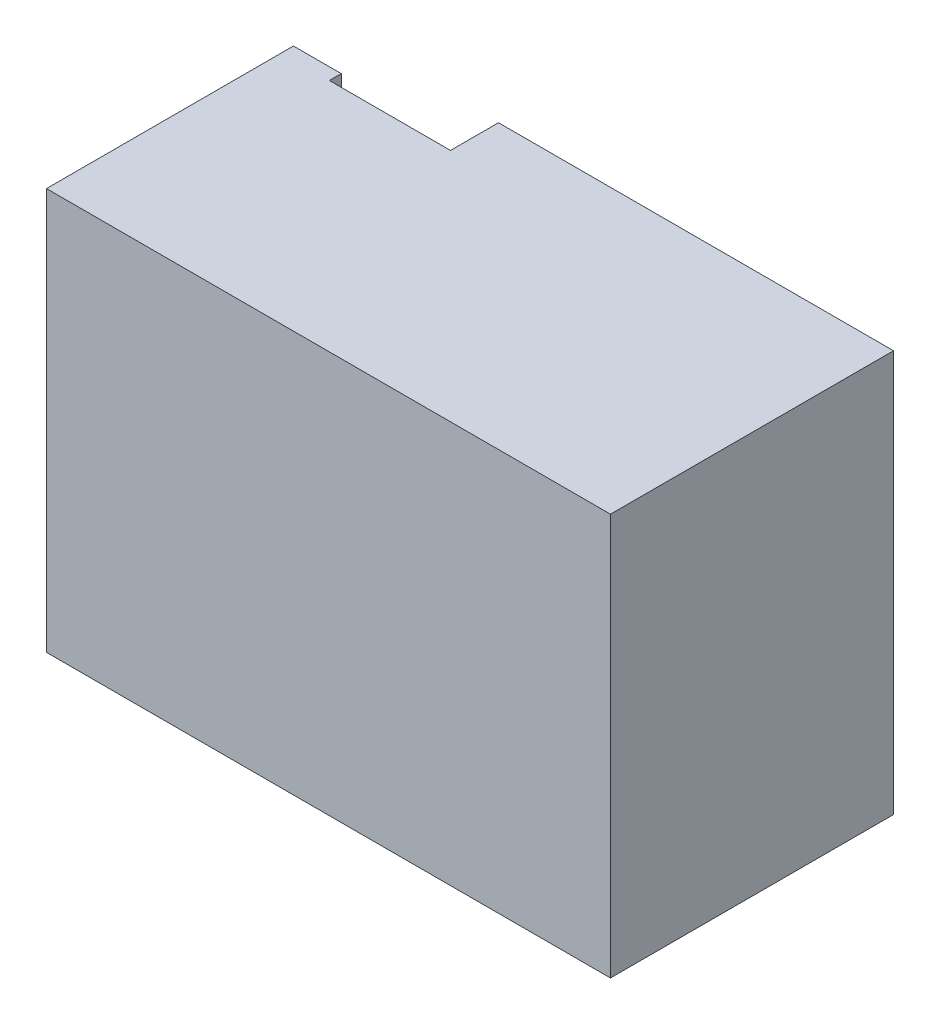
SolidWorks part; units mm, degrees
ref_plane "Front Plane" through (0, 0, 0) normal (0, 0, 1) x (1, 0, 0)
ref_plane "Top Plane" through (0, 0, 0) normal (0, 1, 0) x (1, 0, 0)
ref_plane "Right Plane" through (0, 0, 0) normal (1, 0, 0) x (0, 0, -1)
sketch "Sketch2" plane through (0, 0, 5.4923) normal (0, 0, 1) x (1, 0, 0)
  line L1 (72.3063, -48.321) -> (-33.8937, -48.321)
  line L2 (72.3063, -48.321) -> (72.3063, 59.679)
  line L3 (72.3063, 59.679) -> (-33.8937, 59.679)
  line L4 (-33.8937, -48.321) -> (-33.8937, 59.679)
extrude "Boss-Extrude1" add sketch "Sketch2" along normal blind 38.1
sketch "Sketch3" plane through (-33.8937, 0, 0) normal (-1, 0, 0) x (0, 0, 1)
  line L0 (43.5923, 59.679) -> (5.4923, 59.679) construction
  line L1 (43.5923, -48.321) -> (18.4023, -48.321)
  line L2 (43.5923, -48.321) -> (43.5923, 59.679)
  line L3 (43.5923, 59.679) -> (18.4023, 59.679)
  line L4 (18.4023, -48.321) -> (18.4023, 59.679)
  line L5 (18.4023, 59.679) -> (18.4023, -48.321) construction
extrude "Boss-Extrude2" add sketch "Sketch3" along normal up to vertex (45.43 mm away)
sketch "Sketch5" plane through (0, 0, 18.4023) normal (0, 0, -1) x (-1, 0, 0)
  line L0 (79.3237, 59.679) -> (33.8937, 59.679) construction
  line L1 (79.3237, -48.321) -> (66.4637, -48.321)
  line L2 (79.3237, -48.321) -> (79.3237, 59.679)
  line L3 (79.3237, 59.679) -> (66.4637, 59.679)
  line L4 (66.4637, -48.321) -> (66.4637, 59.679)
  line L5 (66.4637, -48.321) -> (66.4637, 59.679) construction
extrude "Boss-Extrude4" add sketch "Sketch5" along normal up to vertex (3.2 mm away)
sketch "Sketch6" plane through (0, 0, 43.5923) normal (0, 0, 1) x (1, 0, 0)
  line L1 (72.3063, -48.321) -> (-79.3237, -48.321)
  line L2 (72.3063, -48.321) -> (72.3063, 59.679)
  line L3 (72.3063, 59.679) -> (-79.3237, 59.679)
  line L4 (-79.3237, -48.321) -> (-79.3237, 59.679)
extrude "Cut-Extrude1" cut sketch "Sketch6" against normal blind 21
sketch "Sketch7" plane through (0, 0, 22.5923) normal (0, 0, 1) x (1, 0, 0)
  line L1 (72.3063, -48.321) -> (-79.3237, -48.321)
  line L2 (72.3063, -48.321) -> (72.3063, 59.679)
  line L3 (72.3063, 59.679) -> (-79.3237, 59.679)
  line L4 (-79.3237, -48.321) -> (-79.3237, 59.679)
extrude "Boss-Extrude5" add sketch "Sketch7" along normal blind 59
